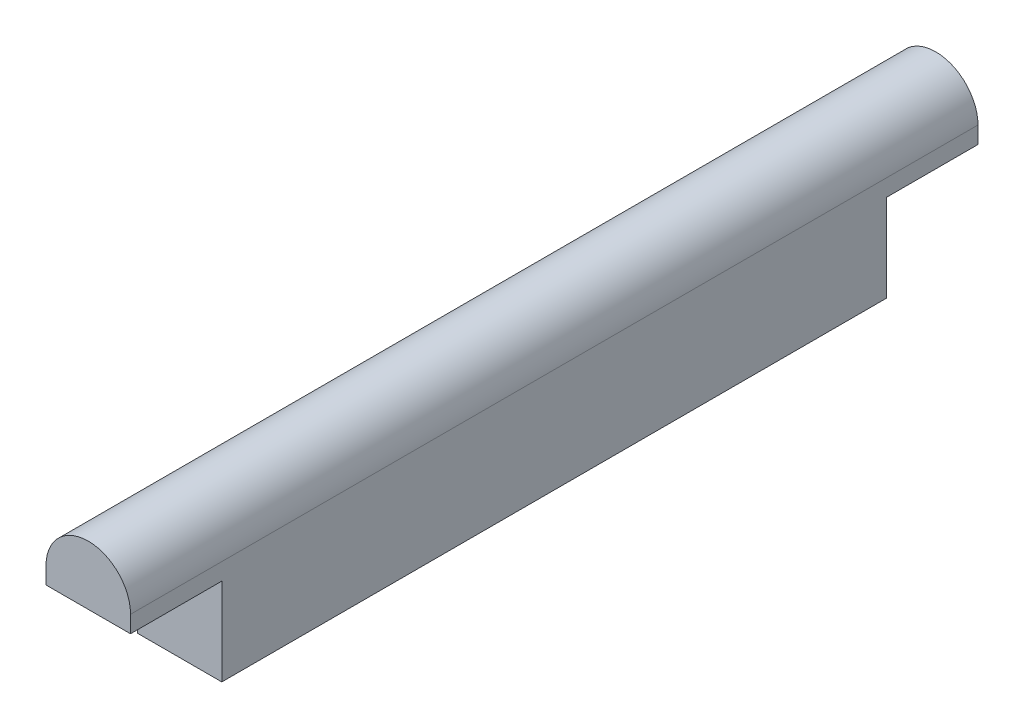
SolidWorks part; units mm, degrees
material "Cedar"
ref_plane "Front Plane" through (0, 0, 0) normal (0, 0, 1) x (1, 0, 0)
ref_plane "Top Plane" through (0, 0, 0) normal (0, 1, 0) x (1, 0, 0)
ref_plane "Right Plane" through (0, 0, 0) normal (1, 0, 0) x (0, 0, -1)
sketch "Sketch1" plane through (0, 0, 0) normal (0, 0, 1) x (1, 0, 0)
  line L1 (-7.5, -7.75) -> (7.5, -7.75)
  line L2 (-7.5, -7.75) -> (-7.5, 7.75)
  line L3 (-7.5, 7.75) -> (7.5, 7.75)
  line L4 (7.5, -7.75) -> (7.5, 7.75)
  line L5 (-7.5, -7.75) -> (7.5, 7.75) construction
  line L6 (-7.5, 7.75) -> (7.5, -7.75) construction
  point P0 (0, 0)
  dimension "D1" = 15
  dimension "D2" = 15.5
extrude "Boss-Extrude1" add sketch "Sketch1" along normal blind 118
sketch "Sketch2" plane through (0, 0, 118) normal (0, 0, 1) x (1, 0, 0)
  line L0 (-7.5, -7.75) -> (7.5, -7.75) construction
  line L3 (-7.5, 7.75) -> (-7.5, 10.75)
  line L4 (0, 7.75) -> (0, 14.6652) construction
  line L5 (7.5, 7.75) -> (-7.5, 7.75) construction
  line L6 (7.5, 7.75) -> (7.5, 10.75)
  line L7 (-7.5, 7.75) -> (7.5, 7.75)
  arc A0 (-7.5, 10.75) -> (7.5, 10.75) centre (0, 10.75) cw
  point P4 (0, 18.25)
  point P5 (0, -7.75)
  dimension "D1" = 3
extrude "Boss-Extrude2" add sketch "Sketch2" along normal blind 16.2 and the other way blind 134.2 contours A0 L6 L7 L3
